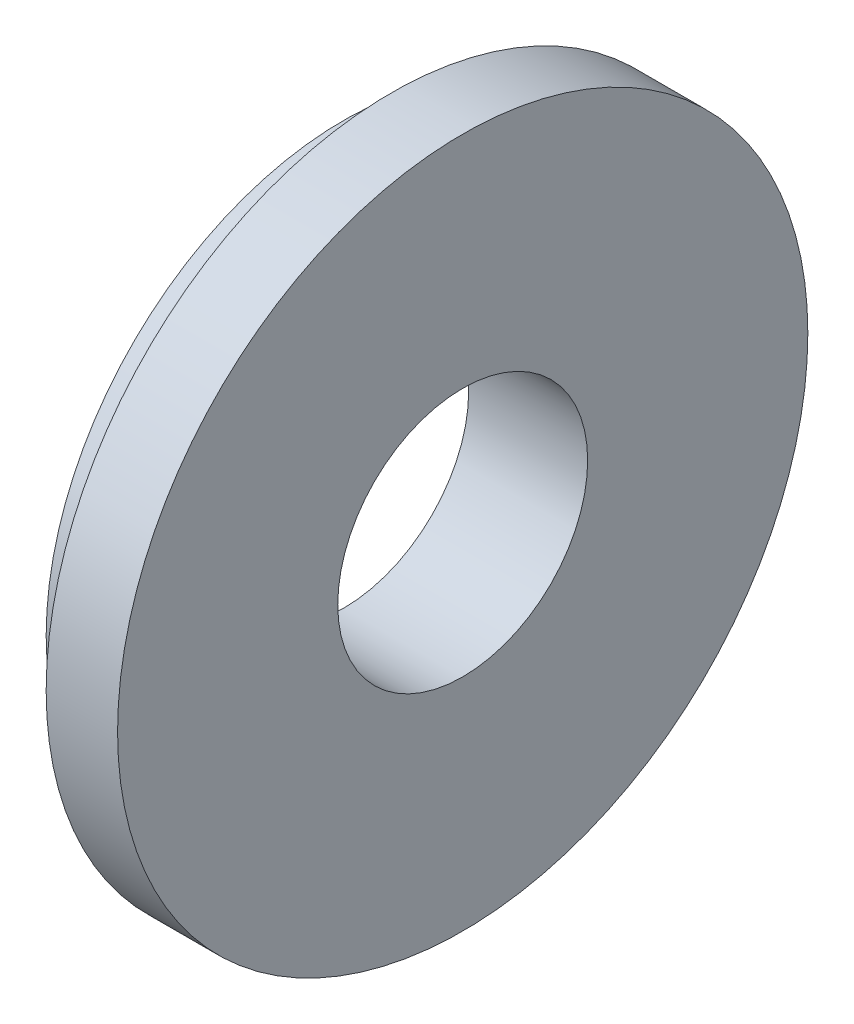
SolidWorks part; units mm, degrees
material "AISI 1020"
ref_plane "Спереди" through (0, 0, 0) normal (0, 0, 1) x (1, 0, 0)
ref_plane "Сверху" through (0, 0, 0) normal (0, 1, 0) x (1, 0, 0)
ref_plane "Справа" through (0, 0, 0) normal (1, 0, 0) x (0, 0, -1)
sketch "Эскиз1" plane through (0, 0, 0) normal (0, 0, 1) x (1, 0, 0)
  line L0 (-1000, 0) -> (49000, 0) construction
  line L1 (0, 0) -> (0, 12.5)
  line L2 (0, -12.5) -> (0, 12.5) construction
  line L3 (0, 12.5) -> (2, 12.5)
  line L4 (2, -20.5) -> (2, 20.5) construction
  line L5 (2, 12.5) -> (2, 14.5)
  line L6 (2, 14.5) -> (5, 14.5)
  line L7 (5, 14.5) -> (5, 0)
  line L8 (5, 0) -> (0, 0)
  line L9 (2, 12.5) -> (-13, 12.5) construction
  dimension "D1" = 2
  dimension "D2" = 3
revolve "Повернуть1" add sketch "Эскиз1" angle 360 about L0
sketch "Эскиз2" plane through (5, 0, 0) normal (1, 0, 0) x (0, 0, -1)
  circle A0 centre (0, 0) radius 5.25
  dimension "D1" = 10.5
extrude "Вырез-Вытянуть1" cut sketch "Эскиз2" against normal through all
